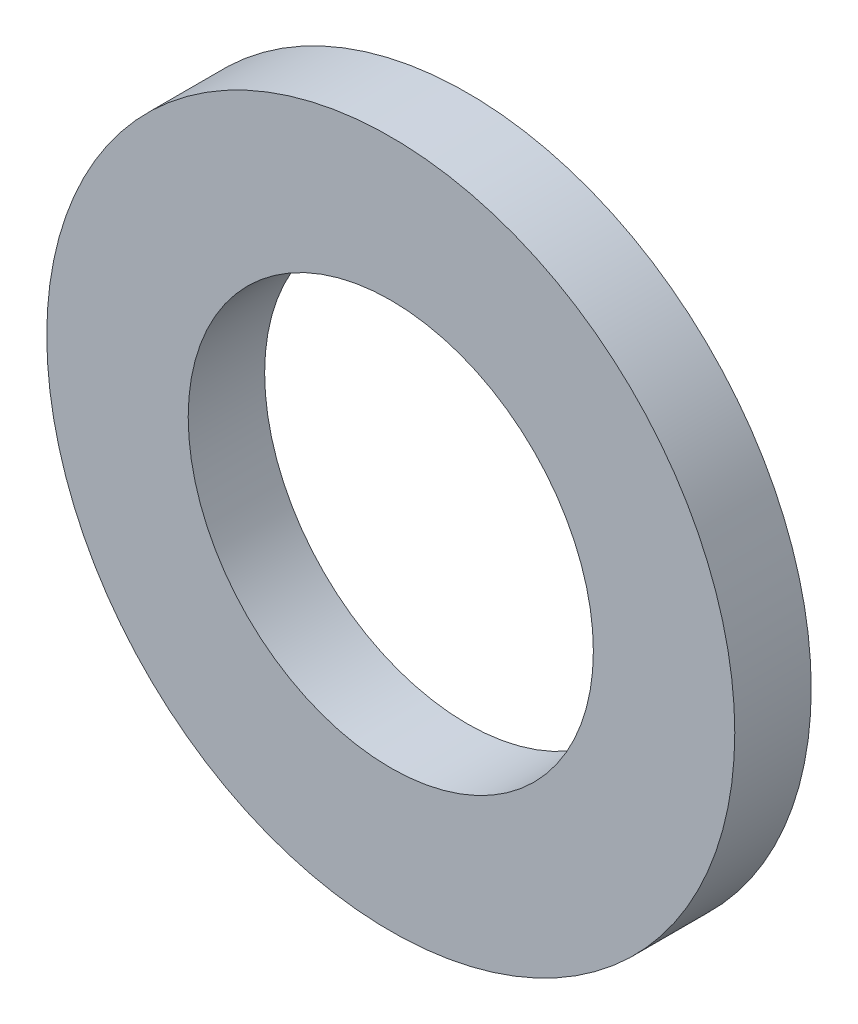
SolidWorks part; units mm, degrees
material "1.4000 (X6Cr13)"
ref_plane "Спереди" through (0, 0, 0) normal (0, 0, 1) x (1, 0, 0)
ref_plane "Сверху" through (0, 0, 0) normal (0, 1, 0) x (1, 0, 0)
ref_plane "Справа" through (0, 0, 0) normal (1, 0, 0) x (0, 0, -1)
sketch "Эскиз1" plane through (0, 0, 0) normal (0, 0, 1) x (1, 0, 0)
  circle A0 centre (0, 0) radius 4.5
  circle A1 centre (0, 0) radius 2.65
  dimension "D1" = 9
  dimension "D2" = 5.3
extrude "Бобышка-Вытянуть1" add sketch "Эскиз1" along normal blind 1
